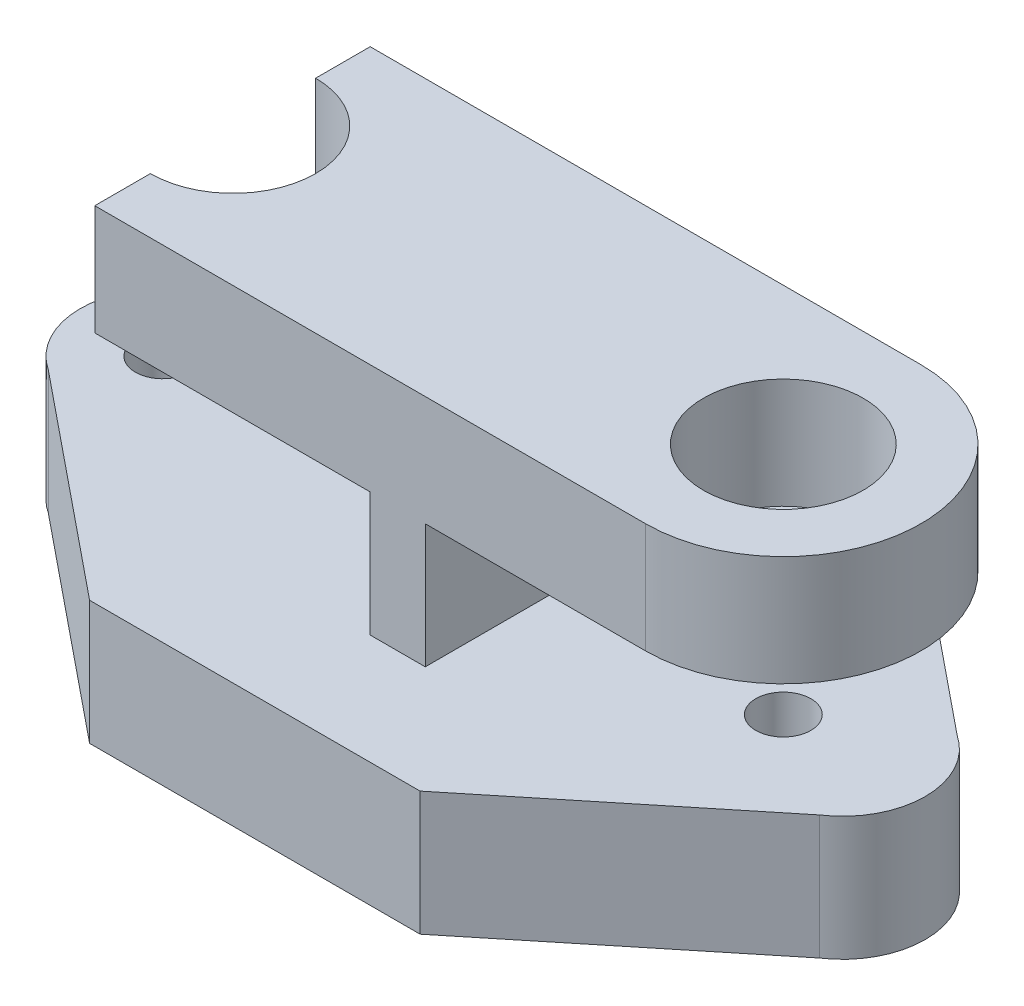
SolidWorks part; units mm, degrees
ref_plane "Front Plane" through (0, 0, 0) normal (0, 0, 1) x (1, 0, 0)
ref_plane "Top Plane" through (0, 0, 0) normal (0, 1, 0) x (1, 0, 0)
ref_plane "Right Plane" through (0, 0, 0) normal (1, 0, 0) x (0, 0, -1)
sketch "Sketch1" plane through (0, 0, -0.3439) normal (0, 1, 0) x (1, 0, 0)
  line L0 (0, -0.0094) -> (6, -0.0094)
  line L1 (0, -0.0094) -> (-4, -3.2594)
  line L2 (-4, -5.7594) -> (0, -9.0094)
  line L3 (0, -9.0094) -> (6, -9.0094)
  line L4 (6, -9.0094) -> (10, -5.7594)
  line L5 (6, -0.0094) -> (10, -3.2594)
  arc A0 (-4, -3.2594) -> (-4, -5.7594) centre (-3.1708, -4.5094) ccw
  arc A1 (10, -3.2594) -> (10, -5.7594) centre (9.1708, -4.5094) cw
  circle A2 centre (-3.1708, -4.5094) radius 0.5
  dimension "D4" = 9
  dimension "D8" = 1.5
  dimension "D11" = 1.5
  dimension "D15" = 1
  dimension "D1" = 6
  dimension "D2" = 4
  dimension "D3" = 3.25
  dimension "D5" = 4
  dimension "D6" = 2.5
  dimension "D7" = 3.25
  dimension "D9" = 4
  dimension "D10" = 3.25
  dimension "D12" = 4
  dimension "D13" = 3.25
  dimension "D16" = 12.3417
extrude "Boss-Extrude1" add sketch "Sketch1" along normal blind 2.25
sketch "Sketch4" plane through (0, 0, 0) normal (0, -1, 0) x (1, 0, 0)
  line L1 (-4.2889, 5.1655) -> (-0.6708, 5.1655)
  line L3 (-4.2889, 3.1655) -> (-0.6708, 3.1655)
  line L5 (0, 8.6655) -> (6, 8.6655) construction
  line L6 (6, -0.3345) -> (0, -0.3345) construction
  line L7 (-0.6708, 5.1655) -> (-0.6708, 3.1655)
  arc A0 (-4, 5.4155) -> (-4, 2.9155) centre (-3.1708, 4.1655) ccw construction
  arc A3 (-4.2889, 3.1655) -> (-4.2889, 5.1655) centre (-3.1708, 4.1655) cw
  dimension "D1" = 3.5
  dimension "D2" = 3.5
  dimension "D3" = 2.5
extrude "Cut-Extrude3" cut sketch "Sketch4" against normal blind 1
sketch "Sketch5" plane through (0, 0, 0) normal (0, -1, 0) x (-1, 0, 0)
  line L1 (0.1708, -7.6655) -> (-6.1708, -7.6655)
  line L2 (0.6708, -7.1655) -> (0.6708, -1.1655)
  line L3 (0.1708, -0.6655) -> (-6.1708, -0.6655)
  line L4 (-6.6708, -7.1655) -> (-6.6708, -1.1655)
  line L6 (0, -8.6655) -> (-6, -8.6655) construction
  line L7 (-6, 0.3345) -> (0, 0.3345) construction
  arc A0 (4.2889, -5.1655) -> (4.2889, -3.1655) centre (3.1708, -4.1655) ccw construction
  arc A1 (-10, -2.9155) -> (-10, -5.4155) centre (-9.1708, -4.1655) ccw construction
  arc A2 (0.1708, -0.6655) -> (0.6708, -1.1655) centre (0.1708, -1.1655) cw
  arc A3 (-6.6708, -1.1655) -> (-6.1708, -0.6655) centre (-6.1708, -1.1655) cw
  arc A4 (-6.1708, -7.6655) -> (-6.6708, -7.1655) centre (-6.1708, -7.1655) cw
  arc A5 (0.1708, -7.6655) -> (0.6708, -7.1655) centre (0.1708, -7.1655) ccw
  dimension "D5" = 0.5
  dimension "D1" = 1
  dimension "D2" = 1
  dimension "D3" = 2.5
  dimension "D4" = 2.5
extrude "Cut-Extrude4" cut sketch "Sketch5" against normal blind 1.25
sketch "Sketch6" plane through (0, 2.25, 0) normal (0, 1, 0) x (1, 0, 0)
  line L0 (6, 0.3345) -> (0, 0.3345) construction
  line L1 (0.5938, -3.9155) -> (3.0938, -3.9155)
  line L2 (0.5938, -3.9155) -> (0.5938, -4.4155)
  line L3 (0.5938, -4.4155) -> (3.0938, -4.4155)
  line L5 (3.0938, -1.6655) -> (4.0938, -1.6655)
  line L6 (3.0938, -1.6655) -> (3.0938, -3.9155)
  line L7 (3.0938, -6.6655) -> (4.0938, -6.6655)
  line L8 (4.0938, -1.6655) -> (4.0938, -6.6655)
  line L10 (0, -8.6655) -> (6, -8.6655) construction
  line L11 (3.0938, -4.4155) -> (3.0938, -6.6655)
  dimension "D1" = 4.25
  dimension "D2" = 4.25
  dimension "D3" = 0.5
  dimension "D4" = 2.5
  dimension "D5" = 5
  dimension "D6" = 2
  dimension "D7" = 2
  dimension "D8" = 1
extrude "Boss-Extrude2" add sketch "Sketch6" along normal blind 2.25
sketch "Sketch7" plane through (0, 4.5, 0) normal (0, 1, 0) x (1, 0, 0)
  line L0 (-1.9062, -1.6655) -> (-1.9062, -2.6561)
  line L1 (-1.9062, -6.6655) -> (8.0938, -6.6655)
  line L2 (-1.9062, -1.6655) -> (8.0938, -1.6655)
  line L3 (0.5938, -3.9155) -> (0.5938, -4.4155) construction
  line L4 (6, 0.3345) -> (0, 0.3345) construction
  line L5 (0, -8.6655) -> (6, -8.6655) construction
  line L6 (-1.9062, -5.6561) -> (-1.9062, -6.6655)
  arc A1 (-1.9062, -2.6561) -> (-1.9062, -5.6561) centre (-1.9062, -4.1561) cw
  arc A2 (8.0938, -1.6655) -> (8.0938, -6.6655) centre (8.0938, -4.1655) cw
  circle A3 centre (8.0938, -4.1655) radius 1
  dimension "D4" = 10
  dimension "D5" = 1.5
  dimension "D7" = 2.5
  dimension "D8" = 2
  dimension "D1" = 2.5
  dimension "D2" = 2
  dimension "D3" = 2
  dimension "D6" = 10
extrude "Boss-Extrude3" add sketch "Sketch7" along normal blind 2
sketch "Sketch8" plane through (0, 2.25, 0) normal (0, 1, 0) x (1, 0, 0)
  circle A0 centre (8.0938, -4.1655) radius 0.5
  dimension "D1" = 1
extrude "Cut-Extrude5" cut sketch "Sketch8" against normal blind 3
hole_wizard "M3.5 Tapped Hole1" positions "3DSketch2" profile "Sketch10" tap size "M3.5" standard "ISO"
sketch3d "3DSketch2"
  line L0 (8.0938, 6.5, 4.1655) -> (8.0938, 4.5, 4.1655) construction
  point P0 (8.0938, 6.5, 4.1655)
sketch "Sketch10" plane through (8.0938, 6.5, 4.1655) normal (1, 0, 0) x (0, 0, 1)
  line L0 (0, 0) -> (0, 2.8712)
  line L1 (0, 2.8712) -> (1.45, 2)
  line L2 (1.45, 2) -> (1.45, 0)
  line L5 (1.45, 0) -> (0, 0)
  line L10 (0, 2.8712) -> (-1.45, 2) construction
  line L11 (0, -6.35) -> (0, 107.95) construction
  dimension "Tap Drill Dia." = 2.9
  dimension "Tap Drill Depth" = 2
  dimension "Drill Angle" = 118
